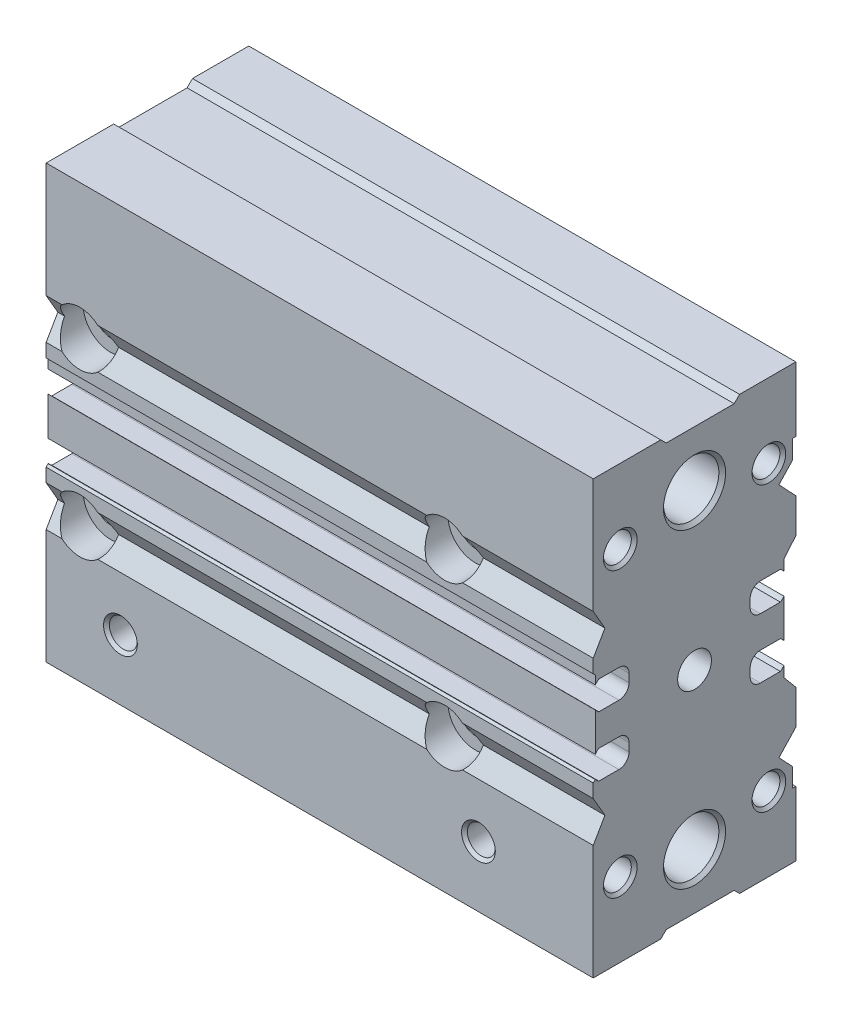
SolidWorks part; units mm, degrees
ref_plane "Front" through (0, 0, 0) normal (0, 0, 1) x (1, 0, 0)
ref_plane "Top" through (0, 0, 0) normal (0, 1, 0) x (1, 0, 0)
ref_plane "Right" through (0, 0, 0) normal (1, 0, 0) x (0, 0, -1)
ref_plane "Plane1" through (0, 0, 0) normal (1, 0, 0) x (0, 0, -1)
sketch "Sketch1" plane through (0, 0, 0) normal (1, 0, 0) x (0, 0, -1)
  line L0 (-15, -32) -> (-5, -32)
  line L1 (-5, -32) -> (-4.2, -31.2)
  line L2 (-4.2, -31.2) -> (5.8667, -31.2)
  line L3 (5.8667, -31.2) -> (6.6667, -32)
  line L4 (6.6667, -32) -> (15, -32)
  line L5 (15, -32) -> (15, -22.4348)
  line L6 (15, -22.4348) -> (14.5, -22.4348)
  line L7 (14.5, -22.4348) -> (14.5, -19.6333)
  line L8 (14.5, -19.6333) -> (12.5, -17.5)
  line L9 (12.5, -17.5) -> (15, -14.8333)
  line L10 (15, -14.8333) -> (15, -9.7142)
  line L11 (15, -9.7142) -> (13.2353, -7.6111)
  line L12 (13.2353, -7.6111) -> (13.2353, -6.0444)
  line L13 (12.7067, -6.5444) -> (9.7353, -6.5444)
  line L14 (8.2353, -5.0444) -> (8.2353, -3.8444)
  line L15 (9.7353, -2.3444) -> (12.7067, -2.3444)
  line L16 (13.2353, -2.8444) -> (13.2353, 2.8444)
  line L17 (12.7067, 2.3444) -> (9.7353, 2.3444)
  line L18 (8.2353, 3.8444) -> (8.2353, 5.0444)
  line L19 (9.7353, 6.5444) -> (12.7067, 6.5444)
  line L20 (13.2353, 6.0444) -> (13.2353, 7.6111)
  line L21 (13.2353, 7.6111) -> (15, 9.7142)
  line L22 (15, 9.7142) -> (15, 14.8333)
  line L23 (15, 14.8333) -> (12.5, 17.5)
  line L24 (12.5, 17.5) -> (14.5, 19.6333)
  line L25 (14.5, 19.6333) -> (14.5, 22.4348)
  line L26 (14.5, 22.4348) -> (15, 22.4348)
  line L27 (15, 22.4348) -> (15, 32)
  line L28 (15, 32) -> (6.6667, 32)
  line L29 (6.6667, 32) -> (5.8667, 31.2)
  line L30 (5.8667, 31.2) -> (-4.2, 31.2)
  line L31 (-4.2, 31.2) -> (-5, 32)
  line L32 (-5, 32) -> (-15, 32)
  line L33 (-15, 32) -> (-15, 15)
  line L34 (-15, 15) -> (-13.2679, 12)
  line L35 (-13.2679, 12) -> (-15, 9)
  line L36 (-15, 9) -> (-15, 7)
  line L37 (-15, 7) -> (-14.7, 6.7)
  line L38 (-14.7, 6.7) -> (-14.7, 5.42)
  line L39 (-14.1714, 5.92) -> (-11.2, 5.92)
  line L40 (-9.7, 4.42) -> (-9.7, 3.22)
  line L41 (-11.2, 1.72) -> (-14.1714, 1.72)
  line L42 (-14.7, 2.22) -> (-14.7, -3.4689)
  line L43 (-14.1714, -2.9689) -> (-11.2, -2.9689)
  line L44 (-9.7, -4.4689) -> (-9.7, -5.6689)
  line L45 (-11.2, -7.1689) -> (-14.1714, -7.1689)
  line L46 (-14.7, -6.6689) -> (-14.7, -6.7)
  line L47 (-14.7, -6.7) -> (-15, -7)
  line L48 (-15, -7) -> (-15, -9)
  line L49 (-15, -9) -> (-13.2679, -12)
  line L50 (-13.2679, -12) -> (-15, -15)
  line L51 (-15, -15) -> (-15, -32)
  arc A0 (13.2353, -6.0444) -> (12.7067, -6.5444) centre (11.221, -4.4444) cw
  arc A1 (9.7353, -6.5444) -> (8.2353, -5.0444) centre (9.7353, -5.0444) cw
  arc A2 (8.2353, -3.8444) -> (9.7353, -2.3444) centre (9.7353, -3.8444) cw
  arc A3 (12.7067, -2.3444) -> (13.2353, -2.8444) centre (11.221, -4.4444) cw
  arc A4 (13.2353, 2.8444) -> (12.7067, 2.3444) centre (11.221, 4.4444) cw
  arc A5 (9.7353, 2.3444) -> (8.2353, 3.8444) centre (9.7353, 3.8444) cw
  arc A6 (8.2353, 5.0444) -> (9.7353, 6.5444) centre (9.7353, 5.0444) cw
  arc A7 (12.7067, 6.5444) -> (13.2353, 6.0444) centre (11.221, 4.4444) cw
  arc A8 (-14.7, 5.42) -> (-14.1714, 5.92) centre (-12.6857, 3.82) cw
  arc A9 (-11.2, 5.92) -> (-9.7, 4.42) centre (-11.2, 4.42) cw
  arc A10 (-9.7, 3.22) -> (-11.2, 1.72) centre (-11.2, 3.22) cw
  arc A11 (-14.1714, 1.72) -> (-14.7, 2.22) centre (-12.6857, 3.82) cw
  arc A12 (-14.7, -3.4689) -> (-14.1714, -2.9689) centre (-12.6857, -5.0689) cw
  arc A13 (-11.2, -2.9689) -> (-9.7, -4.4689) centre (-11.2, -4.4689) cw
  arc A14 (-9.7, -5.6689) -> (-11.2, -7.1689) centre (-11.2, -5.6689) cw
  arc A15 (-14.1714, -7.1689) -> (-14.7, -6.6689) centre (-12.6857, -5.0689) cw
extrude "Boss-Extrude1" add sketch "Sketch1" along normal blind 81
ref_plane "Plane2" through (0, 0, 0) normal (0, 0, 1) x (1, 0, 0)
sketch "Sketch2" plane through (0, 0, 0) normal (0, 0, 1) x (1, 0, 0)
  line L0 (0, 23) -> (0, 27.6)
  line L1 (0, 27.6) -> (0.5, 27.1)
  line L2 (0.5, 27.1) -> (80.5, 27.1)
  line L3 (80.5, 27.1) -> (81, 27.6)
  line L4 (81, 27.6) -> (81, 23)
  line L5 (81, 23) -> (0, 23)
  line L6 (81, 23) -> (0, 23) construction
revolve "Cut-Revolve1" cut sketch "Sketch2" angle 360 about L6
ref_plane "Plane3" through (0, 0, 0) normal (0, 0, 1) x (1, 0, 0)
sketch "Sketch3" plane through (0, 0, 0) normal (0, 0, 1) x (1, 0, 0)
  line L0 (0, -23) -> (0, -18.4)
  line L1 (0, -18.4) -> (0.5, -18.9)
  line L2 (0.5, -18.9) -> (80.5, -18.9)
  line L3 (80.5, -18.9) -> (81, -18.4)
  line L4 (81, -18.4) -> (81, -23)
  line L5 (81, -23) -> (0, -23)
  line L6 (81, -23) -> (0, -23) construction
revolve "Cut-Revolve2" cut sketch "Sketch3" angle 360 about L6
ref_plane "Plane4" through (0, 27, 0) normal (0, 1, 0) x (-1, 0, 0)
sketch "Sketch4" plane through (0, 27, 0) normal (0, 1, 0) x (-1, 0, 0)
  line L0 (-11, -15) -> (-13.5, -15)
  line L1 (-13.5, -15) -> (-13.067, -14.567)
  line L2 (-13.067, -14.567) -> (-13.067, -7.0934)
  line L3 (-13.067, -7.0934) -> (-11, -5.9)
  line L4 (-11, -5.9) -> (-11, -15)
  line L5 (-11, -5.9) -> (-11, -15) construction
revolve "Cut-Revolve3" cut sketch "Sketch4" angle 360 about L5
ref_plane "Plane5" through (0, 27, 0) normal (0, 1, 0) x (-1, 0, 0)
sketch "Sketch5" plane through (0, 27, 0) normal (0, 1, 0) x (-1, 0, 0)
  line L0 (-68, -15) -> (-70.5, -15)
  line L1 (-70.5, -15) -> (-70.067, -14.567)
  line L2 (-70.067, -14.567) -> (-70.067, -7.0934)
  line L3 (-70.067, -7.0934) -> (-68, -5.9)
  line L4 (-68, -5.9) -> (-68, -15)
  line L5 (-68, -5.9) -> (-68, -15) construction
revolve "Cut-Revolve4" cut sketch "Sketch5" angle 360 about L5
ref_plane "Plane6" through (0, -27, 0) normal (0, 1, 0) x (-1, 0, 0)
sketch "Sketch6" plane through (0, -27, 0) normal (0, 1, 0) x (-1, 0, 0)
  line L0 (-11, -15) -> (-13.5, -15)
  line L1 (-13.5, -15) -> (-13.067, -14.567)
  line L2 (-13.067, -14.567) -> (-13.067, -7.0934)
  line L3 (-13.067, -7.0934) -> (-11, -5.9)
  line L4 (-11, -5.9) -> (-11, -15)
  line L5 (-11, -5.9) -> (-11, -15) construction
revolve "Cut-Revolve5" cut sketch "Sketch6" angle 360 about L5
ref_plane "Plane7" through (0, -27, 0) normal (0, 1, 0) x (-1, 0, 0)
sketch "Sketch7" plane through (0, -27, 0) normal (0, 1, 0) x (-1, 0, 0)
  line L0 (-68, -15) -> (-70.5, -15)
  line L1 (-70.5, -15) -> (-70.067, -14.567)
  line L2 (-70.067, -14.567) -> (-70.067, -7.0934)
  line L3 (-70.067, -7.0934) -> (-68, -5.9)
  line L4 (-68, -5.9) -> (-68, -15)
  line L5 (-68, -5.9) -> (-68, -15) construction
revolve "Cut-Revolve6" cut sketch "Sketch7" angle 360 about L5
ref_plane "Plane8" through (0, -23, 0) normal (0, 1, 0) x (-1, 0, 0)
sketch "Sketch8" plane through (0, -23, 0) normal (0, 1, 0) x (-1, 0, 0)
  line L0 (-11, 9.25) -> (-13.067, 9.25)
  line L1 (-13.067, 9.25) -> (-13.067, 14.567)
  line L2 (-13.067, 14.567) -> (-13.5, 15)
  line L3 (-13.5, 15) -> (-11, 15)
  line L4 (-11, 15) -> (-11, 9.25)
  line L5 (-11, 15) -> (-11, 9.25) construction
revolve "Cut-Revolve7" cut sketch "Sketch8" angle 360 about L5
ref_plane "Plane9" through (0, -23, 0) normal (0, 1, 0) x (-1, 0, 0)
sketch "Sketch9" plane through (0, -23, 0) normal (0, 1, 0) x (-1, 0, 0)
  line L0 (-64, 9.25) -> (-66.067, 9.25)
  line L1 (-66.067, 9.25) -> (-66.067, 14.567)
  line L2 (-66.067, 14.567) -> (-66.5, 15)
  line L3 (-66.5, 15) -> (-64, 15)
  line L4 (-64, 15) -> (-64, 9.25)
  line L5 (-64, 15) -> (-64, 9.25) construction
revolve "Cut-Revolve8" cut sketch "Sketch9" angle 360 about L5
ref_plane "Plane10" through (0, 0, 0) normal (0, 1, 0) x (-1, 0, 0)
sketch "Sketch10" plane through (0, 0, 0) normal (0, 1, 0) x (-1, 0, 0)
  line L0 (0, 0) -> (0, -4.1)
  line L1 (0, -4.1) -> (-50, -4.1)
  line L2 (-50, -4.1) -> (-50, 0)
  line L3 (-50, 0) -> (0, 0)
  line L4 (-50, 0) -> (0, 0) construction
revolve "Cut-Revolve9" cut sketch "Sketch10" angle 360 about L4
ref_plane "Plane11" through (11, 0, 0) normal (1, 0, 0) x (0, 0, -1)
sketch "Sketch11" plane through (11, 0, 0) normal (1, 0, 0) x (0, 0, -1)
  line L0 (-10, -26) -> (-7.933, -26)
  line L1 (-7.933, -26) -> (-7.933, -31.567)
  line L2 (-7.933, -31.567) -> (-7.5, -32)
  line L3 (-7.5, -32) -> (-10, -32)
  line L4 (-10, -32) -> (-10, -26)
  line L5 (-10, -32) -> (-10, -26) construction
revolve "Cut-Revolve10" cut sketch "Sketch11" angle 360 about L5
ref_plane "Plane12" through (64, 0, 0) normal (1, 0, 0) x (0, 0, -1)
sketch "Sketch12" plane through (64, 0, 0) normal (1, 0, 0) x (0, 0, -1)
  line L0 (-10, -26) -> (-7.933, -26)
  line L1 (-7.933, -26) -> (-7.933, -31.567)
  line L2 (-7.933, -31.567) -> (-7.5, -32)
  line L3 (-7.5, -32) -> (-10, -32)
  line L4 (-10, -32) -> (-10, -26)
  line L5 (-10, -32) -> (-10, -26) construction
revolve "Cut-Revolve11" cut sketch "Sketch12" angle 360 about L5
ref_plane "Plane13" through (0, 0, 0) normal (0, 0, 1) x (1, 0, 0)
sketch "Sketch13" plane through (0, 0, 0) normal (0, 0, 1) x (1, 0, 0)
  line L0 (71.5566, 0) -> (73, 2.5)
  line L1 (73, 2.5) -> (81, 2.5)
  line L2 (81, 2.5) -> (81, 0)
  line L3 (81, 0) -> (71.5566, 0)
  line L4 (81, 0) -> (71.5566, 0) construction
revolve "Cut-Revolve12" cut sketch "Sketch13" angle 360 about L4
ref_plane "Plane14" through (0, 0, -11) normal (0, 0, 1) x (1, 0, 0)
sketch "Sketch14" plane through (0, 0, -11) normal (0, 0, 1) x (1, 0, 0)
  line L0 (66.6066, 21) -> (67.8, 23.067)
  line L1 (67.8, 23.067) -> (80.567, 23.067)
  line L2 (80.567, 23.067) -> (81, 23.5)
  line L3 (81, 23.5) -> (81, 21)
  line L4 (81, 21) -> (66.6066, 21)
  line L5 (81, 21) -> (66.6066, 21) construction
revolve "Cut-Revolve13" cut sketch "Sketch14" angle 360 about L5
ref_plane "Plane15" through (0, 0, -11) normal (0, 0, 1) x (1, 0, 0)
sketch "Sketch15" plane through (0, 0, -11) normal (0, 0, 1) x (1, 0, 0)
  line L0 (66.6066, -21) -> (67.8, -18.933)
  line L1 (67.8, -18.933) -> (80.567, -18.933)
  line L2 (80.567, -18.933) -> (81, -18.5)
  line L3 (81, -18.5) -> (81, -21)
  line L4 (81, -21) -> (66.6066, -21)
  line L5 (81, -21) -> (66.6066, -21) construction
revolve "Cut-Revolve14" cut sketch "Sketch15" angle 360 about L5
ref_plane "Plane16" through (0, 0, 11) normal (0, 0, 1) x (1, 0, 0)
sketch "Sketch16" plane through (0, 0, 11) normal (0, 0, 1) x (1, 0, 0)
  line L0 (66.6066, 21) -> (67.8, 23.067)
  line L1 (67.8, 23.067) -> (80.567, 23.067)
  line L2 (80.567, 23.067) -> (81, 23.5)
  line L3 (81, 23.5) -> (81, 21)
  line L4 (81, 21) -> (66.6066, 21)
  line L5 (81, 21) -> (66.6066, 21) construction
revolve "Cut-Revolve15" cut sketch "Sketch16" angle 360 about L5
ref_plane "Plane17" through (0, 0, 11) normal (0, 0, 1) x (1, 0, 0)
sketch "Sketch17" plane through (0, 0, 11) normal (0, 0, 1) x (1, 0, 0)
  line L0 (66.6066, -21) -> (67.8, -18.933)
  line L1 (67.8, -18.933) -> (80.567, -18.933)
  line L2 (80.567, -18.933) -> (81, -18.5)
  line L3 (81, -18.5) -> (81, -21)
  line L4 (81, -21) -> (66.6066, -21)
  line L5 (81, -21) -> (66.6066, -21) construction
revolve "Cut-Revolve16" cut sketch "Sketch17" angle 360 about L5
ref_plane "Plane18" through (5, 0, 0) normal (1, 0, 0) x (0, 0, -1)
sketch "Sketch18" plane through (5, 0, 0) normal (1, 0, 0) x (0, 0, -1)
  line L0 (-15, 12) -> (-15, 16)
  line L1 (-15, 16) -> (-10.5, 16)
  line L2 (-10.5, 16) -> (-10.5, 14.15)
  line L3 (-10.5, 14.15) -> (4.3938, 14.15)
  line L4 (4.3938, 14.15) -> (4.3938, 14.067)
  line L5 (4.3938, 14.067) -> (14.567, 14.067)
  line L6 (14.567, 14.067) -> (15, 14.5)
  line L7 (15, 14.5) -> (15, 12)
  line L8 (15, 12) -> (-15, 12)
  line L9 (15, 12) -> (-15, 12) construction
revolve "Cut-Revolve17" cut sketch "Sketch18" angle 360 about L9
ref_plane "Plane19" through (5, 0, 0) normal (1, 0, 0) x (0, 0, -1)
sketch "Sketch19" plane through (5, 0, 0) normal (1, 0, 0) x (0, 0, -1)
  line L0 (-15, -12) -> (-15, -8)
  line L1 (-15, -8) -> (-10.5, -8)
  line L2 (-10.5, -8) -> (-10.5, -9.85)
  line L3 (-10.5, -9.85) -> (4.3938, -9.85)
  line L4 (4.3938, -9.85) -> (4.3938, -9.933)
  line L5 (4.3938, -9.933) -> (14.567, -9.933)
  line L6 (14.567, -9.933) -> (15, -9.5)
  line L7 (15, -9.5) -> (15, -12)
  line L8 (15, -12) -> (-15, -12)
  line L9 (15, -12) -> (-15, -12) construction
revolve "Cut-Revolve18" cut sketch "Sketch19" angle 360 about L9
ref_plane "Plane20" through (59, 0, 0) normal (1, 0, 0) x (0, 0, -1)
sketch "Sketch20" plane through (59, 0, 0) normal (1, 0, 0) x (0, 0, -1)
  line L0 (-15, -12) -> (-15, -8)
  line L1 (-15, -8) -> (-10.5, -8)
  line L2 (-10.5, -8) -> (-10.5, -9.85)
  line L3 (-10.5, -9.85) -> (4.3938, -9.85)
  line L4 (4.3938, -9.85) -> (4.3938, -9.933)
  line L5 (4.3938, -9.933) -> (14.567, -9.933)
  line L6 (14.567, -9.933) -> (15, -9.5)
  line L7 (15, -9.5) -> (15, -12)
  line L8 (15, -12) -> (-15, -12)
  line L9 (15, -12) -> (-15, -12) construction
revolve "Cut-Revolve19" cut sketch "Sketch20" angle 360 about L9
ref_plane "Plane21" through (59, 0, 0) normal (1, 0, 0) x (0, 0, -1)
sketch "Sketch21" plane through (59, 0, 0) normal (1, 0, 0) x (0, 0, -1)
  line L0 (-15, 12) -> (-15, 16)
  line L1 (-15, 16) -> (-10.5, 16)
  line L2 (-10.5, 16) -> (-10.5, 14.15)
  line L3 (-10.5, 14.15) -> (4.3938, 14.15)
  line L4 (4.3938, 14.15) -> (4.3938, 14.067)
  line L5 (4.3938, 14.067) -> (14.567, 14.067)
  line L6 (14.567, 14.067) -> (15, 14.5)
  line L7 (15, 14.5) -> (15, 12)
  line L8 (15, 12) -> (-15, 12)
  line L9 (15, 12) -> (-15, 12) construction
revolve "Cut-Revolve20" cut sketch "Sketch21" angle 360 about L9
